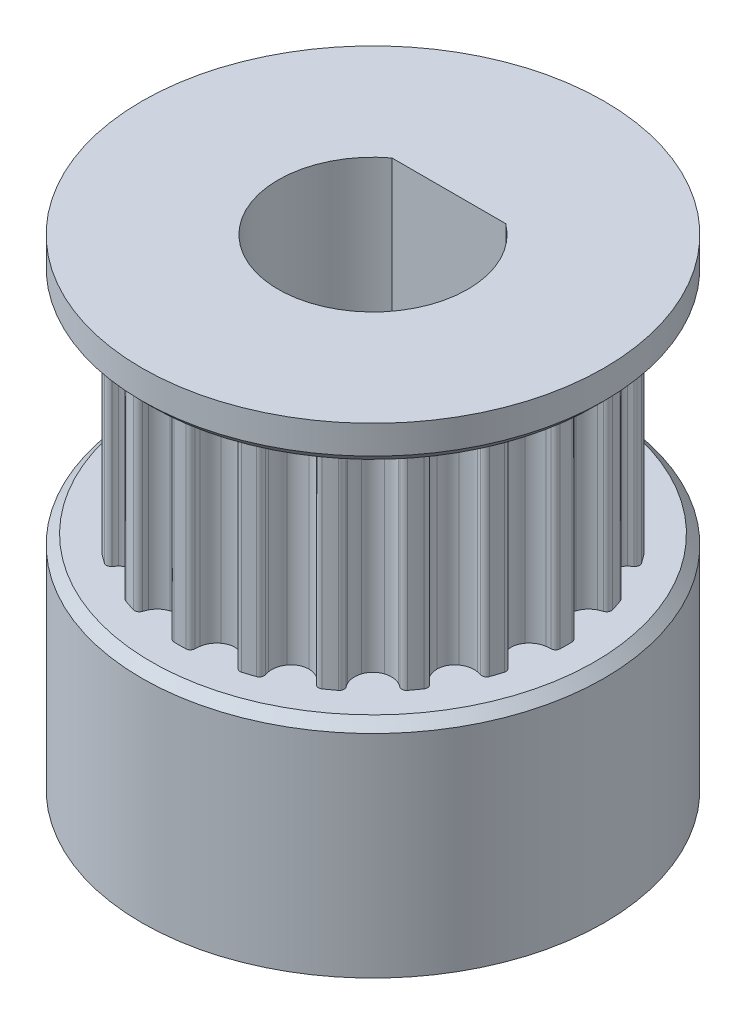
SolidWorks part; units mm, degrees
ref_plane "Front Plane" through (0, 0, 0) normal (0, 0, 1) x (1, 0, 0)
ref_plane "Top Plane" through (0, 0, 0) normal (0, 1, 0) x (1, 0, 0)
ref_plane "Right Plane" through (0, 0, 0) normal (1, 0, 0) x (0, 0, -1)
sketch "Sketch1" plane through (0, 0, 0) normal (0, 1, 0) x (1, 0, 0)
  line L0 (0, 0) -> (0, 6.3662) construction
  line L1 (0, 0) -> (0.9959, 6.2878) construction
  line L2 (0, 0) -> (1.3887, 6.2129) construction
  circle A0 centre (0, 0) radius 6.3662 construction
  circle A1 centre (0, 0) radius 5.3622 construction
  circle A2 centre (0, 0) radius 6.1122 construction
  arc A3 (0.8388, 5.2962) -> (0.5917, 5.401) centre (0.9257, 5.8443) cw
  arc A4 (0.3445, 5.8158) -> (0.3333, 5.9601) centre (1.3333, 5.965) cw
  circle A5 centre (0, 0) radius 5.9622 construction
  arc A6 (-0.188, 6.1093) -> (0.188, 6.1093) centre (0, 0) cw
  arc A7 (0.188, 6.1093) -> (0.3333, 5.9601) centre (0.1833, 5.9594) cw
  arc A8 (0.3445, 5.8158) -> (0.5917, 5.401) centre (0.9759, 5.9111) ccw
  arc A9 (-0.8388, 5.2962) -> (-0.5917, 5.401) centre (-0.9257, 5.8443) ccw
  arc A10 (-0.3445, 5.8158) -> (-0.5917, 5.401) centre (-0.9759, 5.9111) cw
  arc A11 (-0.3445, 5.8158) -> (-0.3333, 5.9601) centre (-1.3333, 5.965) ccw
  arc A12 (-0.188, 6.1093) -> (-0.3333, 5.9601) centre (-0.1833, 5.9594) ccw
  arc A13 (-0.8388, 5.2962) -> (0.8388, 5.2962) centre (0, 0) cw
  point P13 (1.3333, 5.965)
  point P16 (0, 6.1122)
  dimension "D1" = 12.7324
  dimension "D6" = 0.555
  dimension "D7" = 1
  dimension "D9" = 0.15
  dimension "D2" = 9
  dimension "D3" = 3.6
  dimension "D4" = 1.004
  dimension "D5" = 0.75
  dimension "D8" = 0.15
extrude "Boss-Extrude1" add sketch "Sketch1" along normal blind 7 contours A9 A13 A3 A8 A4 A7 A6 A12 A11 A10
sketch "Sketch2" plane through (0, 0, 0) normal (0, -1, 0) x (1, 0, 0)
  circle A0 centre (0, 0) radius 5.3622
  arc A2 (-0.8388, -5.2962) -> (0.8388, -5.2962) centre (0, 0) ccw construction
  arc A5 (-0.8388, -5.2962) -> (0.8388, -5.2962) centre (0, 0) ccw
  arc M3 (-0.8388, -5.2962) -> (-0.5917, -5.401) centre (-0.9257, -5.8443) cw
  arc M4 (-0.5917, -5.401) -> (-0.3445, -5.8158) centre (-0.9759, -5.9111) cw
  arc M5 (-0.3445, -5.8158) -> (-0.3333, -5.9601) centre (-1.3333, -5.965) cw
  arc M6 (-0.3333, -5.9601) -> (-0.188, -6.1093) centre (-0.1833, -5.9594) ccw
  arc M7 (-0.188, -6.1093) -> (0.188, -6.1093) centre (0, 0) ccw
  arc M8 (0.188, -6.1093) -> (0.3333, -5.9601) centre (0.1833, -5.9594) ccw
  arc M9 (0.3333, -5.9601) -> (0.3445, -5.8158) centre (1.3333, -5.965) cw
  arc M10 (0.3445, -5.8158) -> (0.5917, -5.401) centre (0.9759, -5.9111) cw
  arc M11 (0.5917, -5.401) -> (0.8388, -5.2962) centre (0.9257, -5.8443) cw
  arc M12 (0.8388, -5.2962) -> (-0.8388, -5.2962) centre (0, 0) cw
extrude "Boss-Extrude2" add sketch "Sketch2" against normal blind 7 contours A0 M3 M12 M11 M10 M9 M8 M7 M6 M5 M4
pattern_circular "CirPattern3" count 20 over 360 about axis through (0, 0, 0) along (0, 1, 0) of "Boss-Extrude1"
sketch "Sketch3" plane through (0, 7, 0) normal (0, 1, 0) x (1, 0, 0)
  circle A0 centre (0, 0) radius 7.3122
  arc A3 (0.2249, 7.3087) -> (-0.2249, 7.3087) centre (0, 0) ccw
  arc A4 (0.2249, 7.3087) -> (-0.2249, 7.3087) centre (0, 0) ccw
  dimension "D1" = 1.2
extrude "Boss-Extrude3" add sketch "Sketch3" along normal blind 1.2 contours A0
sketch "Sketch4" plane through (0, 0, 0) normal (0, -1, 0) x (1, 0, 0)
  circle A0 centre (0, 0) radius 7.3122 construction
  circle A1 centre (0, 0) radius 7.3122
extrude "Boss-Extrude4" add sketch "Sketch4" along normal blind 7
sketch "Sketch5" plane through (0, 8.2, 0) normal (0, 1, 0) x (1, 0, 0)
  line L0 (0, 0) -> (0, 2.4) construction
  line L1 (1.8, 2.4) -> (-1.8, 2.4)
  arc A0 (-1.8, 2.4) -> (1.8, 2.4) centre (0, 0) ccw
  point P7 (0, 2.4)
  dimension "D1" = 6
  dimension "D2" = 3.6
extrude "Cut-Extrude1" cut sketch "Sketch5" against normal through all
chamfer "Chamfer1" distance 0.3 angle 45 2 edges at (0, 7, 7.3122) (0, 0, -7.3122)
equation "\"TeethNumber\"= 20"
equation "\"Pitch\"= 2"
equation "\"PullyDiameter\"= \"TeethNumber\" * \"Pitch\" / PI"
equation "\"ToothAngle\"= ( 360 / \"TeethNumber\" ) * 1deg"
equation "\"TransOffsetAngle\"= \"ToothAngle\" * 0.2' "
equation "\"ShoulderRadius\"= 0.15"
equation "\"RootRadius\"= 0.555"
equation "\"TransRadius\"= 1"
equation "\"ToothHeight\"= 0.75"
equation "\"PLD\"= 0.254"
equation "\"D1@Sketch1\"=\"PullyDiameter\""
equation "\"D2@Sketch1\"=\"ToothAngle\"/2"
equation "\"D3@Sketch1\"=\"TransOffsetAngle\""
equation "\"D4@Sketch1\"=\"PLD\"+\"ToothHeight\""
equation "\"D5@Sketch1\"=\"ToothHeight\""
equation "\"D6@Sketch1\" = \"RootRadius\""
equation "\"D7@Sketch1\"=\"TransRadius\""
equation "\"D9@Sketch1\"=\"ShoulderRadius\""
